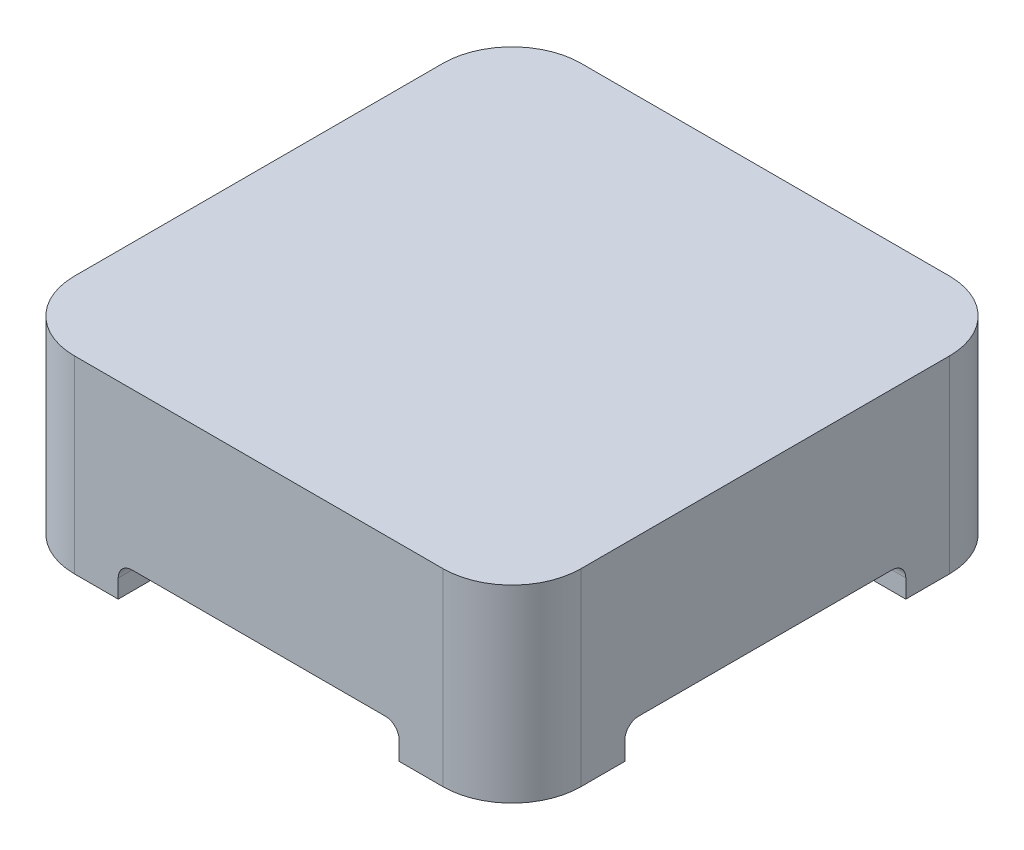
SolidWorks part; units mm, degrees
material "PVC hart"
ref_plane "Ebene vorne" through (0, 0, 0) normal (0, 0, 1) x (1, 0, 0)
ref_plane "Ebene oben" through (0, 0, 0) normal (0, 1, 0) x (1, 0, 0)
ref_plane "Ebene rechts" through (0, 0, 0) normal (1, 0, 0) x (0, 0, -1)
sketch "Skizze1" plane through (0, 0, 0) normal (0, 1, 0) x (1, 0, 0)
  line L1 (-55, 55) -> (55, 55)
  line L2 (-55, 55) -> (-55, -55)
  line L3 (-55, -55) -> (55, -55)
  line L4 (55, 55) -> (55, -55)
  line L5 (-55, 55) -> (55, -55) construction
  line L6 (-55, -55) -> (55, 55) construction
  point P0 (0, 0)
  dimension "D1" = 110
extrude "Aufsatz-Linear austragen1" add sketch "Skizze1" against normal blind 41
fillet "Verrundung1" radius 15 4 edges at (-55, -20.5, -55) (-55, -20.5, 55) (55, -20.5, -55) (55, -20.5, 55)
sketch "Skizze2" plane through (0, 0, 55) normal (0, 0, 1) x (1, 0, 0)
  line L0 (-30.5, -41) -> (-30.5, -37)
  line L1 (-40, -41) -> (40, -41) construction
  line L2 (-27.5, -34) -> (27.5, -34)
  line L3 (30.5, -37) -> (30.5, -41)
  line L4 (0, -41) -> (0, -34) construction
  line L5 (-30.5, -41) -> (30.5, -41)
  arc A0 (-30.5, -37) -> (-27.5, -34) centre (-27.5, -37) cw
  arc A1 (27.5, -34) -> (30.5, -37) centre (27.5, -37) cw
  dimension "D1" = 7
  dimension "D2" = 55
  dimension "D3" = 61
extrude "Schnitt-Linear austragen1" cut sketch "Skizze2" against normal through all
ref_axis "Achse1" through (0, -43.05, 0) along (0, 1, 0)
pattern_circular "Kreismuster1" count 2 over 90 about axis through (0, -43.05, 0) along (0, 1, 0) of "Schnitt-Linear austragen1"
